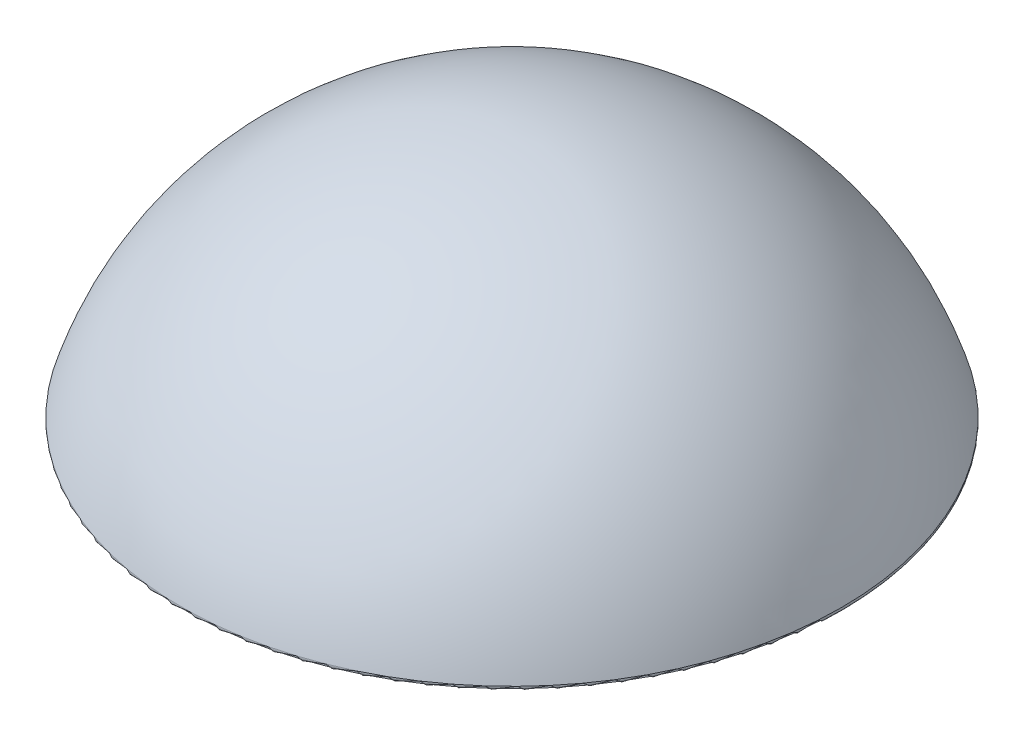
SolidWorks part; units mm, degrees
ref_plane "Front Plane" through (0, 0, 0) normal (0, 0, 1) x (1, 0, 0)
ref_plane "Top Plane" through (0, 0, 0) normal (0, 1, 0) x (1, 0, 0)
ref_plane "Right Plane" through (0, 0, 0) normal (1, 0, 0) x (0, 0, -1)
sketch "Sketch1" plane through (0, 0, 0) normal (0, 0, 1) x (1, 0, 0)
  line L0 (0, 0) -> (0, 37.46)
  line L1 (0, -44.7868) -> (0, 44.7868) construction
  line L2 (0, 0) -> (50, 0)
  line L3 (55, 0) -> (-55, 0) construction
  arc A0 (0, 37.46) -> (50, 0) centre (0, -14.6389) cw
  dimension "D1" = 37.46
  dimension "D2" = 50
revolve "Revolve1" add sketch "Sketch1" angle 360 about L0
fillet "Fillet2" radius 0.5 1 edges at (0, 0, -50)
